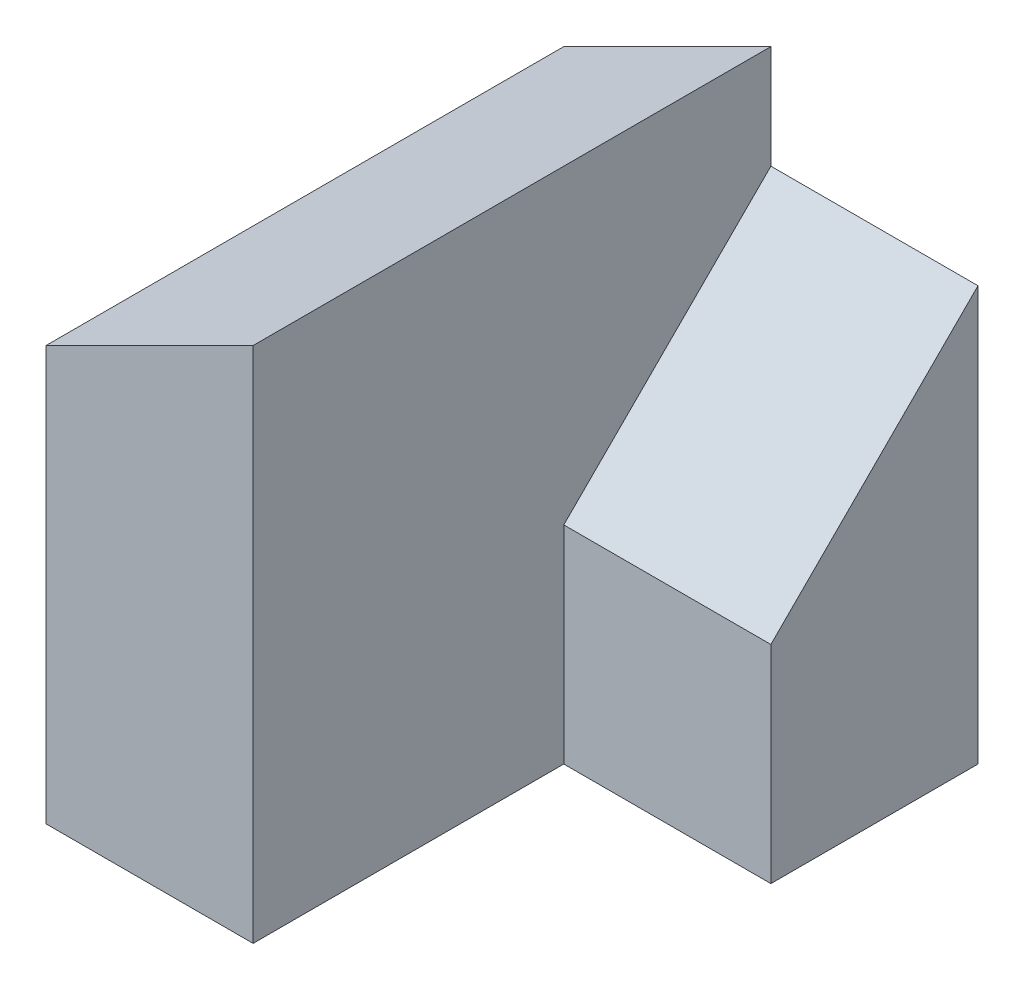
SolidWorks part; units mm, degrees
ref_plane "Front Plane" through (0, 0, 0) normal (0, 0, 1) x (1, 0, 0)
ref_plane "Top Plane" through (0, 0, 0) normal (0, 1, 0) x (1, 0, 0)
ref_plane "Right Plane" through (0, 0, 0) normal (1, 0, 0) x (0, 0, -1)
sketch "Sketch1" plane through (0, 0, 0) normal (0, 0, 1) x (1, 0, 0)
  line L1 (0, 0) -> (10, 0)
  line L2 (0, 0) -> (0, 25)
  line L3 (0, 25) -> (10, 25)
  line L4 (10, 0) -> (10, 25)
  dimension "D1" = 10
  dimension "D2" = 25
extrude "Boss-Extrude1" add sketch "Sketch1" along normal blind 25
sketch "Sketch2" plane through (10, 0, 0) normal (1, 0, 0) x (0, 0, -1)
  line L1 (0, 0) -> (-10, 0)
  line L2 (0, 0) -> (0, 20)
  line L3 (0, 20) -> (-10, 20)
  line L4 (-10, 0) -> (-10, 20)
  dimension "D1" = 20
  dimension "D2" = 10
extrude "Boss-Extrude2" add sketch "Sketch2" along normal blind 10
sketch "Sketch3" plane through (0, 0, 25) normal (0, 0, 1) x (1, 0, 0)
  line L0 (10, 25) -> (0, 20)
  line L1 (0, 25) -> (0, 0) construction
  line L2 (0, 20) -> (0, 25)
  line L3 (0, 25) -> (10, 25)
  dimension "D1" = 5
extrude "Cut-Extrude1" cut sketch "Sketch3" against normal blind 40
sketch "Sketch4" plane through (20, 0, 0) normal (1, 0, 0) x (0, 0, -1)
  line L0 (-10, 10) -> (0, 20)
  line L1 (-10, 20) -> (-10, 0) construction
  line L2 (0, 20) -> (-10, 20)
  line L3 (-10, 20) -> (-10, 10)
extrude "Cut-Extrude2" cut sketch "Sketch4" against normal blind 10
sketch "Sketch5" plane through (0, 0, 0) normal (-1, 0, 0) x (0, 0, 1)
  line L1 (0, 0) -> (15, 0)
  line L2 (0, 0) -> (0, 10)
  line L3 (0, 10) -> (15, 10)
  line L4 (15, 0) -> (15, 10)
  dimension "D1" = 15
  dimension "D2" = 10
extrude "Boss-Extrude3" add sketch "Sketch5" along normal blind 10
